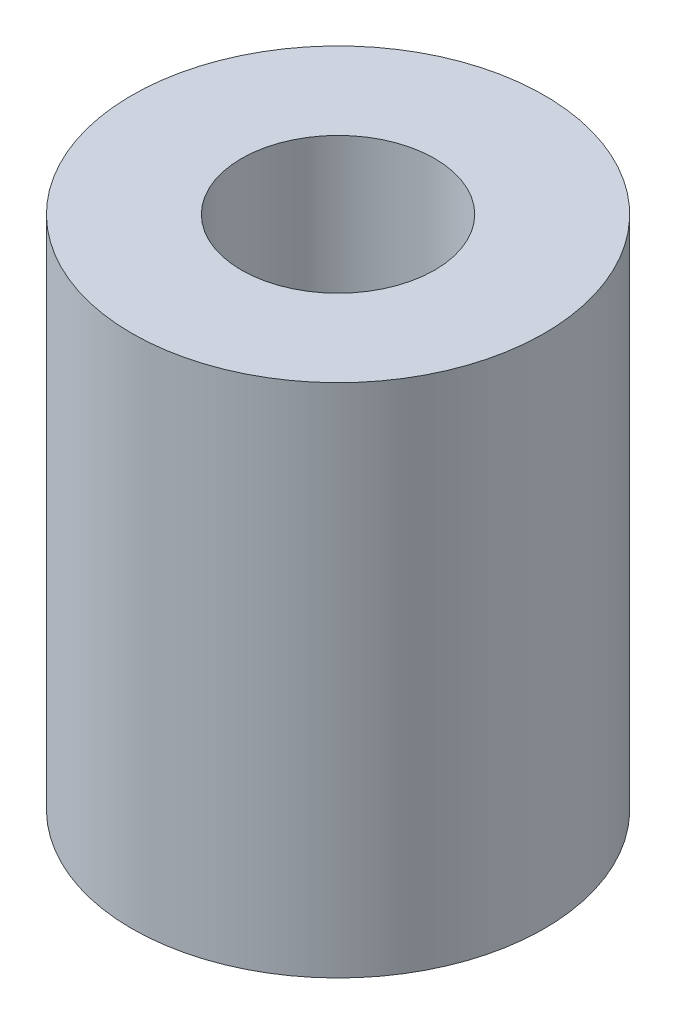
SolidWorks part; units mm, degrees
ref_plane "前视基准面" through (0, 0, 0) normal (0, 0, 1) x (1, 0, 0)
ref_plane "上视基准面" through (0, 0, 0) normal (0, 1, 0) x (1, 0, 0)
ref_plane "右视基准面" through (0, 0, 0) normal (1, 0, 0) x (0, 0, -1)
sketch "草图1" plane through (0, 0, 0) normal (0, 1, 0) x (1, 0, 0)
  circle A0 centre (0, 0) radius 7
  circle A1 centre (0, 0) radius 16
  dimension "D1" = 14
  dimension "D2" = 32
extrude "凸台-拉伸1" add sketch "草图1" along normal blind 40
ref_plane "基准面2" through (0, 40, 0) normal (0, 1, 0) x (1, 0, 0)
sketch "草图3" plane through (0, 40, 0) normal (0, 1, 0) x (1, 0, 0)
  circle A0 centre (0, 0) radius 7.5
  dimension "D1" = 15
extrude "切除-拉伸1" cut sketch "草图3" against normal blind 20
